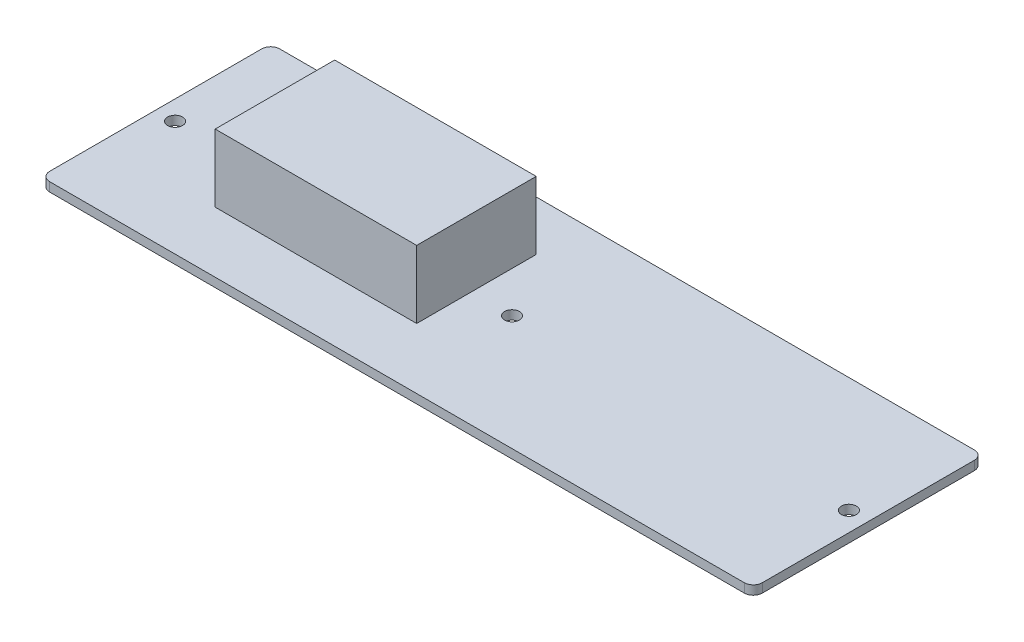
SolidWorks part; units mm, degrees
ref_plane "Front Plane" through (0, 0, 0) normal (0, 0, 1) x (1, 0, 0)
ref_plane "Top Plane" through (0, 0, 0) normal (0, 1, 0) x (1, 0, 0)
ref_plane "Right Plane" through (0, 0, 0) normal (1, 0, 0) x (0, 0, -1)
sketch "Sketch1" plane through (0, 0, 0) normal (0, 1, 0) x (1, 0, 0)
  line L1 (0, 0) -> (158, 0)
  line L2 (0, 0) -> (0, 51)
  line L3 (0, 51) -> (158, 51)
  line L4 (158, 0) -> (158, 51)
  dimension "D1" = 51
  dimension "D2" = 158
extrude "Boss-Extrude1" add sketch "Sketch1" along normal blind 2
sketch "Sketch2" plane through (0, 2, 0) normal (0, 1, 0) x (1, 0, 0)
  line L0 (0, 25.5) -> (158, 25.5) construction
  line L1 (0, 51) -> (0, 0) construction
  line L2 (158, 0) -> (158, 51) construction
  line L3 (79, 0) -> (79, 51) construction
  line L4 (0, 0) -> (158, 0) construction
  line L5 (158, 51) -> (0, 51) construction
  circle A0 centre (4.3, 25.5) radius 1.65
  circle A1 centre (153.7, 25.5) radius 1.65
  circle A2 centre (79, 25.5) radius 1.65
  dimension "D1" = 3.3
  dimension "D2" = 4.3
  dimension "D3" = 3.3
extrude "Cut-Extrude1" cut sketch "Sketch2" against normal through all
fillet "Fillet1" radius 2 4 edges at (158, 1, 0) (158, 1, -51) (0, 1, -51) (0, 1, 0)
sketch "Sketch3" plane through (0, 2, 0) normal (0, 1, 0) x (1, 0, 0)
  line L1 (25.2314, 13.4541) -> (69.9108, 13.4541)
  line L2 (25.2314, 13.4541) -> (25.2314, 39.9551)
  line L3 (25.2314, 39.9551) -> (69.9108, 39.9551)
  line L4 (69.9108, 13.4541) -> (69.9108, 39.9551)
extrude "Boss-Extrude2" add sketch "Sketch3" along normal blind 15
